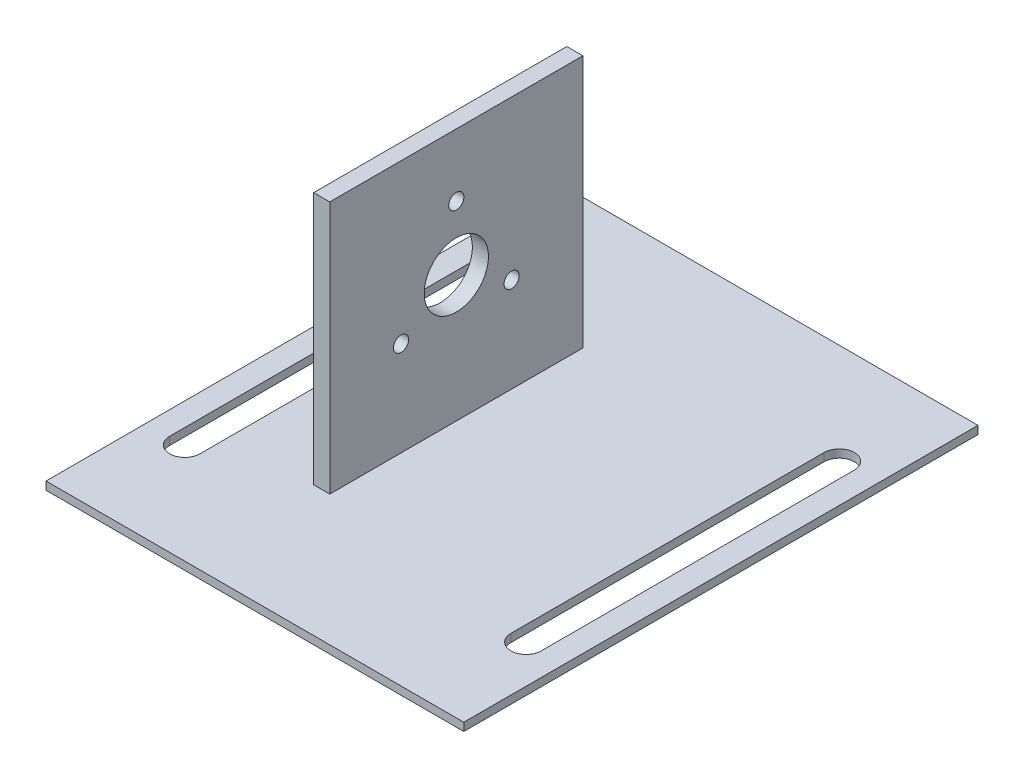
SolidWorks part; units mm, degrees
ref_plane "Front Plane" through (0, 0, 0) normal (0, 0, 1) x (1, 0, 0)
ref_plane "Top Plane" through (0, 0, 0) normal (0, 1, 0) x (1, 0, 0)
ref_plane "Right Plane" through (0, 0, 0) normal (1, 0, 0) x (0, 0, -1)
sketch "Sketch1" plane through (0, 0, 0) normal (0, 1, 0) x (1, 0, 0)
  line L1 (0, 0) -> (165.1, 0)
  line L2 (0, 0) -> (0, 203.2)
  line L3 (0, 203.2) -> (165.1, 203.2)
  line L4 (165.1, 0) -> (165.1, 203.2)
  dimension "D1" = 165.1
  dimension "D2" = 203.2
extrude "Boss-Extrude1" add sketch "Sketch1" along normal blind 3.175
sketch "Sketch2" plane through (0, 3.175, 0) normal (0, 1, 0) x (-1, 0, 0)
  line L0 (-15.113, -203.2) -> (-15.113, 0) construction
  line L1 (-165.1, -203.2) -> (0, -203.2) construction
  line L2 (0, 0) -> (-165.1, 0) construction
  line L3 (-149.987, -203.2) -> (-149.987, 0) construction
  line L4 (0, -101.6) -> (-165.1, -101.6) construction
  line L5 (0, -203.2) -> (0, 0) construction
  line L6 (-165.1, 0) -> (-165.1, -203.2) construction
  line L7 (-149.987, -86.1141) -> (-165.1, -86.1141) construction
  line L8 (-15.113, -86.1141) -> (0, -86.1141) construction
  line L9 (-15.113, -39.7389) -> (-15.113, -163.4611) construction
  line L10 (-9.113, -39.7389) -> (-9.113, -163.4611)
  line L11 (-21.113, -39.7389) -> (-21.113, -163.4611)
  line L12 (-149.987, -39.7389) -> (-149.987, -163.4611) construction
  line L13 (-143.987, -39.7389) -> (-143.987, -163.4611)
  line L14 (-155.987, -39.7389) -> (-155.987, -163.4611)
  arc A2 (-9.113, -39.7389) -> (-21.113, -39.7389) centre (-15.113, -39.7389) ccw
  arc A3 (-21.113, -163.4611) -> (-9.113, -163.4611) centre (-15.113, -163.4611) ccw
  arc A4 (-143.987, -39.7389) -> (-155.987, -39.7389) centre (-149.987, -39.7389) ccw
  arc A5 (-155.987, -163.4611) -> (-143.987, -163.4611) centre (-149.987, -163.4611) ccw
  point P24 (-15.113, -101.6)
  point P30 (-149.987, -101.6)
  dimension "D2" = 123.7223
  dimension "D3" = 6
  dimension "D1" = 134.874
extrude "Cut-Extrude1" cut sketch "Sketch2" against normal through all
sketch "Sketch3" plane through (0, 3.175, 0) normal (0, 1, 0) x (-1, 0, 0)
  line L1 (-54.1997, -51.6) -> (-60.5497, -51.6)
  line L2 (-54.1997, -51.6) -> (-54.1997, -151.6)
  line L3 (-54.1997, -151.6) -> (-60.5497, -151.6)
  line L4 (-60.5497, -51.6) -> (-60.5497, -151.6)
  line L5 (-54.1997, -51.6) -> (-60.5497, -151.6) construction
  line L6 (-54.1997, -151.6) -> (-60.5497, -51.6) construction
  point P0 (-57.3747, -101.6)
extrude "Boss-Extrude2" add sketch "Sketch3" along normal blind 100
sketch "Sketch4" plane through (60.5497, 0, 0) normal (1, 0, 0) x (0, 0, -1)
  line L0 (101.6, 53.175) -> (123.444, 40.5634) construction
  line L1 (101.6, 53.175) -> (79.756, 40.5634) construction
  line L3 (101.6, 103.175) -> (101.6, 3.175) construction
  line L4 (51.6, 103.175) -> (151.6, 103.175) construction
  line L5 (0, 3.175) -> (203.2, 3.175) construction
  line L6 (151.6, 53.175) -> (51.6, 53.175) construction
  line L7 (151.6, 103.175) -> (151.6, 3.175) construction
  line L8 (51.6, 103.175) -> (51.6, 3.175) construction
  line L9 (101.6, 78.3983) -> (101.6, 53.175) construction
  circle A0 centre (101.6, 53.175) radius 12.7
  point P21 (101.6, 53.175)
  point P22 (79.756, 40.5634)
  point P23 (123.444, 40.5634)
  point P24 (101.6, 78.3983)
  dimension "D5" = 25.4
  dimension "D1" = 43.688
  dimension "D2" = 43.688
  dimension "D3" = 120
  dimension "D4" = 120
hole_wizard "Ø6.0 (6) Diameter Hole1" positions "3DSketch1" profile "Sketch5" hole size "Ø6.0" standard "Ansi Metric" end condition through all
sketch3d "3DSketch1"
  line L0 (60.5497, 78.3983, -101.6) -> (60.5497, 40.5634, -123.444) construction
  line L1 (60.5497, 40.5634, -123.444) -> (60.5497, 40.5634, -79.756) construction
  line L2 (60.5497, 40.5634, -79.756) -> (60.5497, 78.3983, -101.6) construction
  line L5 (60.5497, 59.4808, -112.522) -> (60.5497, 48.1701, -92.9313) construction
  line L8 (60.5497, 59.4808, -90.678) -> (60.5497, 50.0592, -106.9967) construction
  line L11 (60.5497, 40.5634, -101.6) -> (60.5497, 60.628, -101.6) construction
  point P0 (60.5497, 78.3983, -101.6)
  point P3 (60.5497, 40.5634, -79.756)
  point P6 (60.5497, 40.5634, -123.444)
sketch "Sketch5" plane through (60.5497, 78.3983, -101.6) normal (0, 1, 0) x (0, 0, -1)
  line L0 (0, 0) -> (0, 60.5497)
  line L1 (0, 60.5497) -> (3, 60.5497)
  line L2 (3, 60.5497) -> (3, 0)
  line L5 (3, 0) -> (0, 0)
  line L11 (0, -6.35) -> (0, 107.95) construction
  dimension "Thru Hole Dia." = 6
  dimension "Thru Hole Depth" = 60.5497
extrude "Cut-Extrude2" cut sketch "Sketch4" against normal through all
